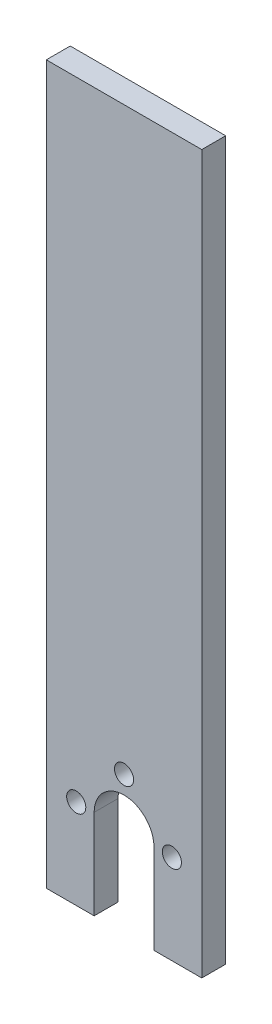
SolidWorks part; units mm, degrees
ref_plane "前视基准面" through (0, 0, 0) normal (0, 0, 1) x (1, 0, 0)
ref_plane "上视基准面" through (0, 0, 0) normal (0, 1, 0) x (1, 0, 0)
ref_plane "右视基准面" through (0, 0, 0) normal (1, 0, 0) x (0, 0, -1)
sketch "草图1" plane through (0, 0, 0) normal (0, 0, 1) x (1, 0, 0)
  line L0 (0, 0) -> (0, 12.8875) construction
  line L2 (-8, -15) -> (-13, -15)
  line L3 (-13, -15) -> (-13, -12)
  line L5 (5, 0) -> (5, -15)
  line L6 (-5, 0) -> (-5, -15)
  line L7 (-5, -15) -> (-8, -15)
  line L8 (8, -15) -> (13, -15)
  line L9 (5, -15) -> (8, -15)
  line L10 (13, -15) -> (13, -12)
  line L14 (-11, 105) -> (11, 105)
  line L16 (-13, -12) -> (-13, 105)
  line L17 (-13, 105) -> (-11, 105)
  line L18 (13, -12) -> (13, 105)
  line L19 (13, 105) -> (11, 105)
  arc A0 (5, 0) -> (-5, 0) centre (0, 0) ccw
  circle A1 centre (8, 0) radius 1.6
  circle A2 centre (-8, 0) radius 1.6
  circle A3 centre (0, 8) radius 1.6
  dimension "D1" = 10
  dimension "D6" = 8
  dimension "D7" = 8
  dimension "D2" = 15
  dimension "D4" = 3
  dimension "D5" = 5
  dimension "D8" = 120
extrude "凸台-拉伸1" add sketch "草图1" along normal blind 4
